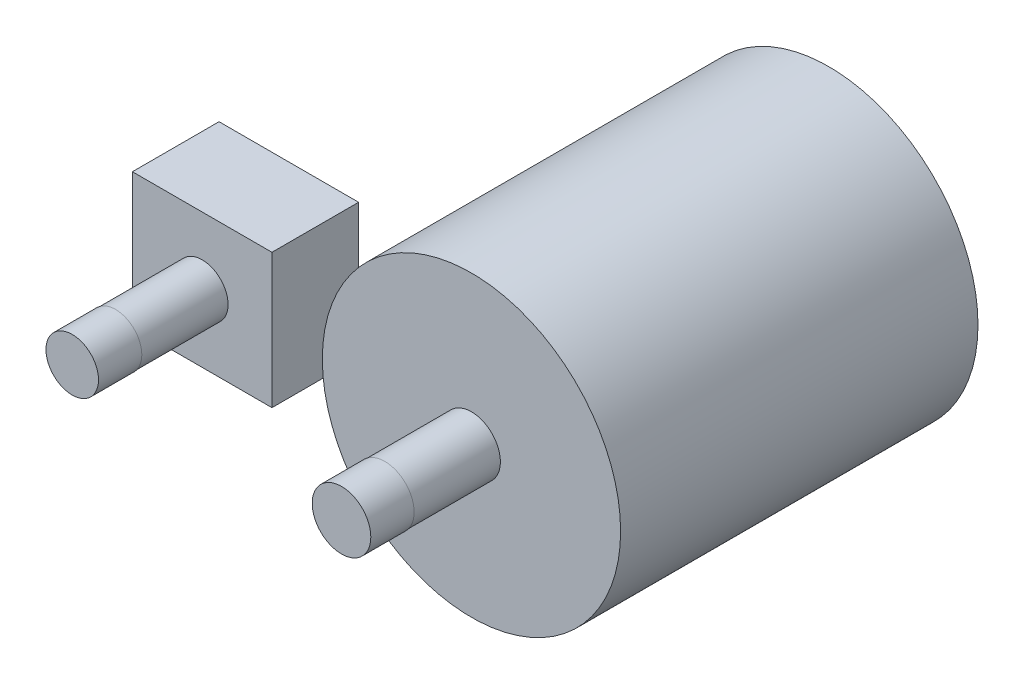
SolidWorks part; units mm, degrees
ref_plane "Front Plane" through (0, 0, 0) normal (0, 0, 1) x (1, 0, 0)
ref_plane "Top Plane" through (0, 0, 0) normal (0, 1, 0) x (1, 0, 0)
ref_plane "Right Plane" through (0, 0, 0) normal (1, 0, 0) x (0, 0, -1)
sketch "Sketch2" plane through (0, 0, 0) normal (0, 0, 1) x (1, 0, 0)
  circle A0 centre (0, 0) radius 13.7713
extrude "Boss-Extrude1" add sketch "Sketch2" along normal blind 33
sketch "Sketch4" plane through (0, 0, 33) normal (0, 0, 1) x (1, 0, 0)
  circle A0 centre (0, 0) radius 2.6705
extrude "Boss-Extrude2" add sketch "Sketch4" along normal blind 8
sketch "Sketch5" plane through (0, 0, 33) normal (0, 0, 1) x (1, 0, 0)
  line L0 (0, 0) -> (-24.8647, 0)
  circle A0 centre (-24.8647, 0) radius 2.3918
extrude "Boss-Extrude3" add sketch "Sketch5" along normal blind 8 separate body
sketch "Sketch6" plane through (0, 0, 33) normal (0, 0, -1) x (-1, 0, 0)
  line L1 (18.4224, -6.2138) -> (31.3071, -6.2138)
  line L2 (18.4224, -6.2138) -> (18.4224, 6.2138)
  line L3 (18.4224, 6.2138) -> (31.3071, 6.2138)
  line L4 (31.3071, -6.2138) -> (31.3071, 6.2138)
  line L5 (18.4224, -6.2138) -> (31.3071, 6.2138) construction
  line L6 (18.4224, 6.2138) -> (31.3071, -6.2138) construction
  point P0 (24.8647, 0)
extrude "Boss-Extrude4" add sketch "Sketch6" along normal blind 8
sketch "Sketch20" plane through (0, 0, 41) normal (0, 0, 1) x (1, 0, 0)
sketch "Sketch23" plane through (0, 0, 41) normal (0, 0, 1) x (1, 0, 0)
  circle A0 centre (-24.8647, 0) radius 2.426
extrude "Boss-Extrude6" add sketch "Sketch23" along normal blind 4
sketch "Sketch24" plane through (0, 0, 41) normal (0, 0, 1) x (1, 0, 0)
  circle A0 centre (0, 0) radius 2.7046
extrude "Boss-Extrude7" add sketch "Sketch24" along normal blind 4
sketch "Sketch25" plane through (0, 0, 45) normal (0, 0, 1) x (1, 0, 0)
  line L0 (0, 2.7046) -> (-24.8647, 2.426)
  line L1 (-24.8647, -2.426) -> (0, -2.7046)
  circle A0 centre (0, 0) radius 2.7046 construction
  circle A1 centre (-24.8647, 0) radius 2.426 construction
sketch "Sketch26" plane through (0, 0, 41) normal (0, 0, -1) x (-1, 0, 0)
  line L0 (24.8647, 2.426) -> (0, 2.7046)
  circle A0 centre (24.8647, 0) radius 2.426 construction
  circle A1 centre (0, 0) radius 2.7046 construction
